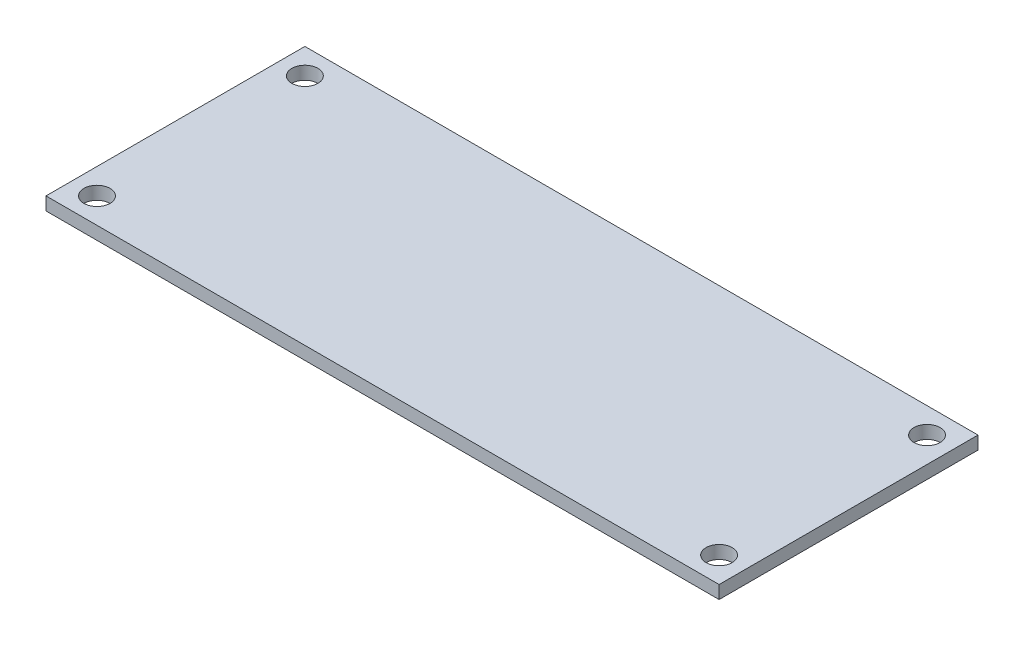
SolidWorks part; units mm, degrees
ref_plane "Front Plane" through (0, 0, 0) normal (0, 0, 1) x (1, 0, 0)
ref_plane "Top Plane" through (0, 0, 0) normal (0, 1, 0) x (1, 0, 0)
ref_plane "Right Plane" through (0, 0, 0) normal (1, 0, 0) x (0, 0, -1)
sketch "Sketch1" plane through (0, 0, 0) normal (0, 1, 0) x (1, 0, 0)
  line L0 (-38.15, -12.75) -> (-38.15, 12.75) construction
  line L1 (-41.275, -15.875) -> (41.275, -15.875)
  line L2 (-41.275, -15.875) -> (-41.275, 15.875)
  line L3 (-41.275, 15.875) -> (41.275, 15.875)
  line L4 (41.275, -15.875) -> (41.275, 15.875)
  line L5 (-41.275, -15.875) -> (41.275, 15.875) construction
  line L6 (-41.275, 15.875) -> (41.275, -15.875) construction
  line L7 (-38.15, 12.75) -> (38.15, 12.75) construction
  line L8 (38.15, -12.75) -> (38.15, 12.75) construction
  line L9 (-38.15, -12.75) -> (38.15, -12.75) construction
  circle A0 centre (-38.15, 12.75) radius 1.6
  circle A1 centre (38.15, 12.75) radius 1.6
  circle A2 centre (38.15, -12.75) radius 1.6
  circle A3 centre (-38.15, -12.75) radius 1.6
  point P0 (0, 0)
  dimension "D4" = 3.2
  dimension "D1" = 31.75
  dimension "D2" = 82.55
  dimension "D3" = 3.125
extrude "Boss-Extrude1" add sketch "Sketch1" along normal mid plane 1.6
